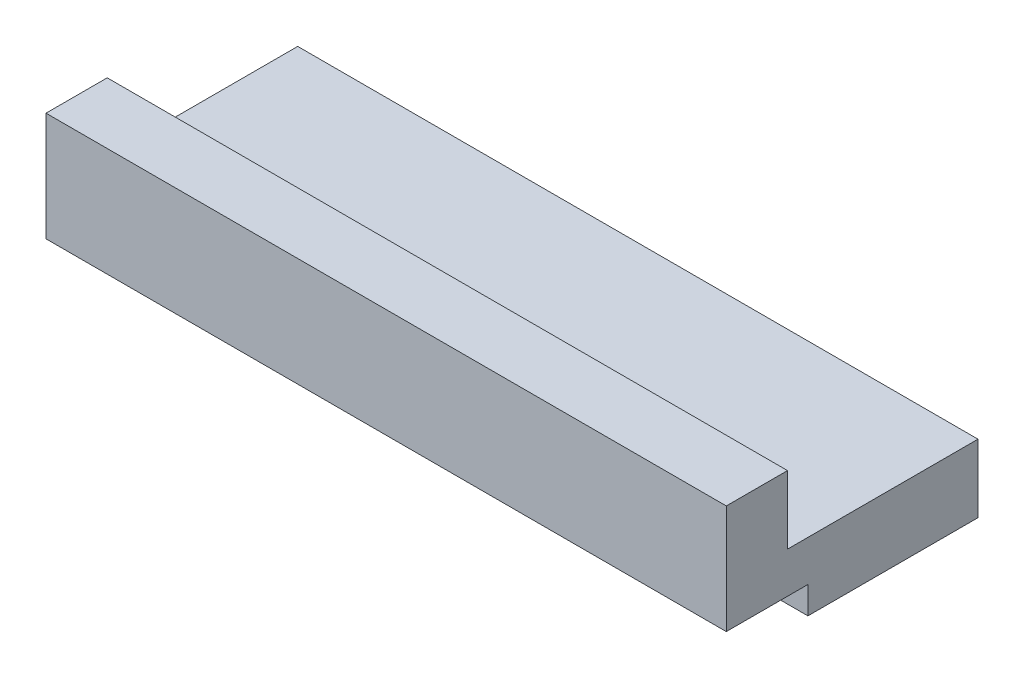
SolidWorks part; units mm, degrees
ref_plane "Front Plane" through (0, 0, 0) normal (0, 0, 1) x (1, 0, 0)
ref_plane "Top Plane" through (0, 0, 0) normal (0, 1, 0) x (1, 0, 0)
ref_plane "Right Plane" through (0, 0, 0) normal (1, 0, 0) x (0, 0, -1)
sketch "Sketch1" plane through (0, 0, 0) normal (0, 1, 0) x (1, 0, 0)
  line L1 (-15.0861, 0.4079) -> (10.3139, 0.4079)
  line L2 (-15.0861, 0.4079) -> (-15.0861, 2.6939)
  line L3 (-15.0861, 2.6939) -> (10.3139, 2.6939)
  line L4 (10.3139, 0.4079) -> (10.3139, 2.6939)
  dimension "D1" = 2.286
  dimension "D2" = 25.4
extrude "Boss-Extrude1" add sketch "Sketch1" along normal blind 4.064
sketch "Sketch2" [suppressed] plane through (0, 4.064, 0) normal (0, 1, 0) x (1, 0, 0)
  line L0 (-27.7861, 2.6939) -> (-27.7861, 0.4079) construction
  line L1 (10.3139, 0.4079) -> (-27.7861, 0.4079)
  line L2 (10.3139, 0.4079) -> (10.3139, 2.6939)
  line L3 (10.3139, 2.6939) -> (-27.7861, 2.6939)
  line L4 (-27.7861, 0.4079) -> (-27.7861, 2.6939)
  point P8 (-27.7861, 1.5509)
sketch "Sketch3" plane through (0, 0, -2.6939) normal (0, 0, -1) x (-1, 0, 0)
  line L0 (-10.3139, 4.064) -> (-10.3139, 0) construction
  line L1 (15.0861, 1.524) -> (-10.3139, 1.524)
  line L2 (15.0861, 1.524) -> (15.0861, -1.016)
  line L3 (15.0861, -1.016) -> (-10.3139, -1.016)
  line L4 (-10.3139, 1.524) -> (-10.3139, -1.016)
  line L5 (15.0861, 4.064) -> (15.0861, 0) construction
  line L6 (-10.3139, 0) -> (15.0861, 0) construction
  point P9 (15.0861, 2.032)
  dimension "D1" = 2.54
  dimension "D2" = 1.524
extrude "Boss-Extrude3" add sketch "Sketch3" along normal blind 7.112
sketch "Sketch4" plane through (-15.0861, 0, 0) normal (-1, 0, 0) x (0, 0, 1)
  line L1 (-2.6939, -1.016) -> (-3.4559, -1.016)
  line L2 (-2.6939, -1.016) -> (-2.6939, 0)
  line L3 (-2.6939, 0) -> (-3.4559, 0)
  line L4 (-3.4559, -1.016) -> (-3.4559, 0)
  dimension "D1" = 0.762
extrude "Cut-Extrude1" cut sketch "Sketch4" against normal blind 30.734
